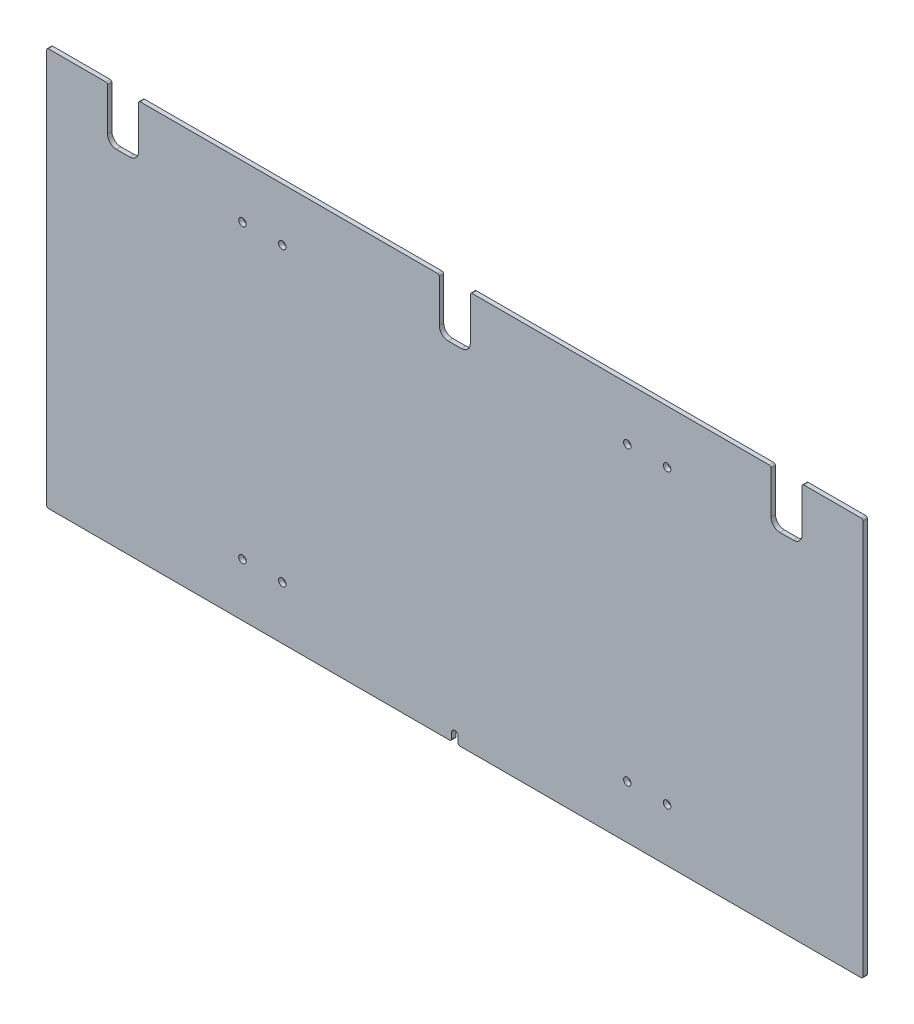
SolidWorks part; units mm, degrees
material "PC High Viscosity"
ref_plane "Front Plane" through (0, 0, 0) normal (0, 0, 1) x (1, 0, 0)
ref_plane "Top Plane" through (0, 0, 0) normal (0, 1, 0) x (1, 0, 0)
ref_plane "Right Plane" through (0, 0, 0) normal (1, 0, 0) x (0, 0, -1)
sketch "Sketch1" plane through (0, 0, 0) normal (0, 0, 1) x (1, 0, 0)
  line L1 (-585.7875, 0) -> (585.7875, 0)
  line L2 (-585.7875, 0) -> (-585.7875, 571.5)
  line L3 (-585.7875, 571.5) -> (585.7875, 571.5)
  line L4 (585.7875, 0) -> (585.7875, 571.5)
  dimension "D1" = 1171.575
  dimension "D2" = 571.5
extrude "Boss-Extrude1" add sketch "Sketch1" along normal blind 6.35
hole_wizard "27/64 (0.42188) Diameter Hole1" positions "Sketch3" profile "Sketch4" hole size "27/64" standard "ANSI Inch" end condition through all
sketch "Sketch3" plane through (0, 0, 6.35) normal (0, 0, 1) x (1, 0, 0)
  line L0 (0, 0) -> (0, 571.5) construction
  line L1 (-585.7875, 0) -> (585.7875, 0) construction
  line L2 (585.7875, 571.5) -> (-585.7875, 571.5) construction
  line L4 (-298.45, 571.5) -> (-254, 571.5) construction
  line L5 (-298.45, 571.5) -> (-298.45, 0) construction
  line L6 (-298.45, 0) -> (-254, 0) construction
  line L7 (-254, 571.5) -> (-254, 0) construction
  line L8 (-276.225, 571.5) -> (-276.225, 0) construction
  line L9 (-585.7875, 285.75) -> (585.7875, 285.75) construction
  line L10 (-585.7875, 571.5) -> (-585.7875, 0) construction
  line L11 (585.7875, 0) -> (585.7875, 571.5) construction
  point P61 (-247.65, 495.3)
  point P75 (-304.8, 495.3)
  point P78 (-247.65, 76.2)
  point P79 (-304.8, 76.2)
  point P81 (247.65, 76.2)
  point P82 (304.8, 76.2)
  point P83 (247.65, 495.3)
  point P84 (304.8, 495.3)
  dimension "D1" = 44.45
  dimension "D2" = 254
  dimension "D3" = 6.35
  dimension "D4" = 76.2
sketch "Sketch4" plane through (304.8, 495.3, 6.35) normal (1, 0, 0) x (0, -1, 0)
  line L0 (0, 0) -> (0, 6.35)
  line L1 (0, 6.35) -> (5.3579, 6.35)
  line L2 (5.3579, 6.35) -> (5.3579, 0)
  line L5 (5.3579, 0) -> (0, 0)
  line L11 (0, -6.35) -> (0, 107.95) construction
  dimension "Thru Hole Dia." = 10.7158
  dimension "Thru Hole Depth" = 6.35
sketch "Sketch5" plane through (0, 0, 6.35) normal (0, 0, 1) x (1, 0, 0)
  line L0 (-498.475, 571.5) -> (-498.475, 495.3)
  line L1 (585.7875, 571.5) -> (-585.7875, 571.5) construction
  line L2 (-454.025, 571.5) -> (-454.025, 495.3)
  line L3 (0, 0) -> (0, 571.5) construction
  line L4 (-454.025, 571.5) -> (-498.475, 571.5)
  line L5 (22.225, 571.5) -> (-22.225, 571.5)
  line L6 (-22.225, 571.5) -> (-22.225, 495.3)
  line L7 (22.225, 571.5) -> (22.225, 495.3)
  line L8 (498.475, 571.5) -> (454.025, 571.5)
  line L9 (454.025, 571.5) -> (454.025, 495.3)
  line L10 (498.475, 571.5) -> (498.475, 495.3)
  line L11 (-585.7875, 527.05) -> (585.7875, 527.05) construction
  line L12 (-585.7875, 571.5) -> (-585.7875, 0) construction
  line L13 (585.7875, 0) -> (585.7875, 571.5) construction
  line L14 (-454.025, 495.3) -> (-498.475, 495.3)
  line L15 (22.225, 495.3) -> (-22.225, 495.3)
  line L16 (498.475, 495.3) -> (454.025, 495.3)
  point P6 (-476.25, 495.3)
  point P20 (0, 495.3)
  point P21 (476.25, 495.3)
  dimension "D2" = 31.75
  dimension "D3" = 44.45
  dimension "D4" = 476.25
  dimension "D5" = 44.45
  dimension "D1" = 3
extrude "Cut-Extrude1" cut sketch "Sketch5" against normal through all
sketch "Sketch6" plane through (0, 0, 6.35) normal (0, 0, 1) x (1, 0, 0)
  line L0 (4.7625, 0) -> (-4.7625, 0)
  line L1 (-585.7875, 0) -> (585.7875, 0) construction
  line L2 (-4.7625, 0) -> (-4.7625, 11.1125)
  line L3 (4.7625, 0) -> (4.7625, 11.1125)
  arc A0 (-4.7625, 11.1125) -> (4.7625, 11.1125) centre (0, 11.1125) cw
  point P9 (0, 15.875)
  dimension "D1" = 15.875
  dimension "D2" = 9.525
extrude "Cut-Extrude2" cut sketch "Sketch6" against normal through all
fillet "Fillet1" radius 12.7 6 edges at (454.025, 495.3, 3.175) (498.475, 495.3, 3.175) (22.225, 495.3, 3.175) (-22.225, 495.3, 3.175) (-498.475, 495.3, 3.175) (-454.025, 495.3, 3.175)
fillet "Fillet2" radius 2.54 12 edges at (-4.7625, 0, 3.175) (-585.7875, 0, 3.175) (-498.475, 571.5, 3.175) (-454.025, 571.5, 3.175) (-22.225, 571.5, 3.175) (22.225, 571.5, 3.175) (454.025, 571.5, 3.175) (498.475, 571.5, 3.175) (585.7875, 571.5, 3.175) (585.7875, 0, 3.175) (4.7625, 0, 3.175) (-585.7875, 571.5, 3.175)
